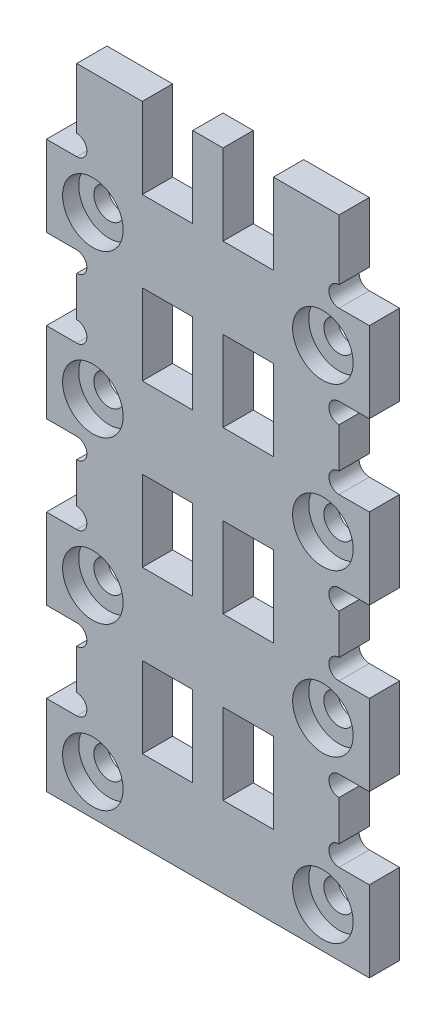
SolidWorks part; units mm, degrees
material "Thornel Mat VMA"
ref_plane "前视基准面" through (0, 0, 0) normal (0, 0, 1) x (1, 0, 0)
ref_plane "上视基准面" through (0, 0, 0) normal (0, 1, 0) x (1, 0, 0)
ref_plane "右视基准面" through (0, 0, 0) normal (1, 0, 0) x (0, 0, -1)
sketch "草图1" plane through (0, 0, 0) normal (0, 0, 1) x (1, 0, 0)
  line L0 (0, 0) -> (0, 16.7389) construction
  line L1 (16, 0) -> (-16, 0)
  line L2 (-16, 0) -> (-16, 8)
  line L3 (-16, 8) -> (-13, 8)
  line L4 (-13, 8) -> (-13, 16)
  line L5 (-13, 16) -> (-16, 16)
  line L6 (-16, 16) -> (-16, 24)
  line L7 (-16, 24) -> (-13, 24)
  line L8 (-13, 24) -> (-13, 32)
  line L9 (-13, 32) -> (-16, 32)
  line L10 (-16, 32) -> (-16, 40)
  line L11 (-16, 40) -> (-13, 40)
  line L12 (-13, 40) -> (-13, 48)
  line L13 (-13, 48) -> (-16, 48)
  line L14 (-16, 48) -> (-16, 56)
  line L15 (-16, 56) -> (-13, 56)
  line L16 (16, 0) -> (16, 8)
  line L17 (16, 8) -> (13, 8)
  line L18 (13, 8) -> (13, 16)
  line L19 (13, 16) -> (16, 16)
  line L20 (16, 16) -> (16, 24)
  line L21 (16, 24) -> (13, 24)
  line L22 (13, 24) -> (13, 32)
  line L23 (13, 32) -> (16, 32)
  line L24 (16, 32) -> (16, 40)
  line L25 (16, 40) -> (13, 40)
  line L26 (13, 40) -> (13, 48)
  line L27 (13, 48) -> (16, 48)
  line L28 (16, 48) -> (16, 56)
  line L29 (-13, 56) -> (-13, 64)
  line L30 (-13, 64) -> (13, 64)
  line L31 (16, 56) -> (13, 56)
  line L32 (13, 56) -> (13, 64)
  point P32 (0, 56)
  point P37 (0, 64)
  dimension "D1" = 16
  dimension "D2" = 8
  dimension "D3" = 3
  dimension "D4" = 8
  dimension "D5" = 8
  dimension "D6" = 8
  dimension "D7" = 8
  dimension "D8" = 3
  dimension "D9" = 8
  dimension "D10" = 8
  dimension "D11" = 16
  dimension "D12" = 8
  dimension "D13" = 3
extrude "凸台-拉伸1" add sketch "草图1" along normal blind 3
sketch "草图2" plane through (0, 0, 3) normal (0, 0, 1) x (1, 0, 0)
  line L0 (-13, 12) -> (13, 12) construction
  line L1 (-13, 16) -> (-13, 8) construction
  line L2 (13, 8) -> (13, 16) construction
  line L3 (-13, 28) -> (13, 28) construction
  line L4 (-13, 32) -> (-13, 24) construction
  line L5 (13, 24) -> (13, 32) construction
  line L6 (-13, 44) -> (13, 44) construction
  line L7 (-13, 48) -> (-13, 40) construction
  line L8 (13, 40) -> (13, 48) construction
  line L9 (-6.5, 32) -> (-6.5, 24)
  line L10 (-6.5, 16) -> (-1.5, 16)
  line L11 (-6.5, 16) -> (-6.5, 8)
  line L12 (-6.5, 8) -> (-1.5, 8)
  line L13 (-1.5, 16) -> (-1.5, 8)
  line L14 (-6.5, 16) -> (-1.5, 8) construction
  line L15 (-6.5, 8) -> (-1.5, 16) construction
  line L16 (-6.5, 32) -> (-1.5, 32)
  line L17 (-1.5, 32) -> (-1.5, 24)
  line L18 (-6.5, 24) -> (-1.5, 24)
  line L19 (1.5, 32) -> (1.5, 24)
  line L20 (6.5, 32) -> (1.5, 32)
  line L21 (6.5, 32) -> (6.5, 24)
  line L22 (6.5, 24) -> (1.5, 24)
  line L23 (0, 12) -> (0, 19.1819) construction
  line L24 (-6.5, 48) -> (-6.5, 40)
  line L25 (-6.5, 48) -> (-1.5, 48)
  line L26 (-1.5, 48) -> (-1.5, 40)
  line L27 (-6.5, 40) -> (-1.5, 40)
  line L28 (1.5, 48) -> (1.5, 40)
  line L29 (6.5, 48) -> (1.5, 48)
  line L30 (6.5, 48) -> (6.5, 40)
  line L31 (6.5, 40) -> (1.5, 40)
  line L32 (6.5, 8) -> (1.5, 8)
  line L33 (6.5, 16) -> (6.5, 8)
  line L34 (1.5, 16) -> (1.5, 8)
  line L35 (6.5, 16) -> (1.5, 16)
  line L36 (0, 64) -> (0, 54.9911) construction
  line L37 (13, 64) -> (-13, 64) construction
  line L38 (0, 60) -> (-4, 60) construction
  line L39 (6.5, 56) -> (1.5, 56)
  line L40 (-6.5, 64) -> (-1.5, 64)
  line L41 (-6.5, 64) -> (-6.5, 56)
  line L42 (-6.5, 56) -> (-1.5, 56)
  line L43 (-1.5, 64) -> (-1.5, 56)
  line L44 (-6.5, 64) -> (-1.5, 56) construction
  line L45 (-6.5, 56) -> (-1.5, 64) construction
  line L46 (1.5, 64) -> (1.5, 56)
  line L47 (6.5, 64) -> (1.5, 64)
  line L48 (6.5, 64) -> (6.5, 56)
  point P18 (0, 12)
  point P19 (0, 28)
  point P20 (0, 44)
  point P21 (-4, 12)
  dimension "D1" = 4
  dimension "D2" = 8
  dimension "D3" = 5
  dimension "D4" = 3
  dimension "D5" = 4
  dimension "D6" = 4
  dimension "D7" = 8
  dimension "D8" = 5
extrude "切除-拉伸1" cut sketch "草图2" against normal blind 3
sketch "草图3" plane through (0, 0, 3) normal (0, 0, 1) x (1, 0, 0)
  line L0 (-16, 4) -> (16, 4) construction
  line L1 (-16, 8) -> (-16, 0) construction
  line L2 (16, 0) -> (16, 8) construction
  line L3 (0, 4) -> (0, 12.4627) construction
  line L4 (-16, 20) -> (16, 20) construction
  line L5 (-16, 24) -> (-16, 16) construction
  line L6 (16, 16) -> (16, 24) construction
  circle A0 centre (-11.4, 4) radius 1.5
  circle A1 centre (11.4, 4) radius 1.5
  circle A2 centre (-11.4, 20) radius 1.5
  circle A3 centre (11.4, 20) radius 1.5
  circle A4 centre (-11.4, 36) radius 1.5
  circle A5 centre (11.4, 36) radius 1.5
  circle A6 centre (-11.4, 52) radius 1.5
  circle A7 centre (11.4, 52) radius 1.5
  point P6 (0, 4)
  point P7 (-11.4, 4)
  dimension "D2" = 3
  dimension "D1" = 11.4
  dimension "D3" = 4
extrude "切除-拉伸2" cut sketch "草图3" against normal blind 3
sketch "草图4" plane through (0, 0, 3) normal (0, 0, 1) x (1, 0, 0)
  circle A0 centre (-11.4, 4) radius 3
  circle A1 centre (11.4, 4) radius 3
  circle A2 centre (-11.4, 20) radius 3
  circle A3 centre (11.4, 20) radius 3
  circle A4 centre (-11.4, 36) radius 3
  circle A5 centre (11.4, 36) radius 3
  circle A6 centre (-11.4, 52) radius 3
  circle A7 centre (11.4, 52) radius 3
  dimension "D1" = 6
  dimension "D2" = 6
  dimension "D3" = 4
extrude "切除-拉伸3" cut sketch "草图4" against normal blind 1.6
sketch "草图5" plane through (0, 0, 3) normal (0, 0, 1) x (1, 0, 0)
  line L0 (-13, 64) -> (-13, 56) construction
  line L1 (-13, 48) -> (-13, 40) construction
  line L2 (-13, 32) -> (-13, 24) construction
  line L3 (-13, 16) -> (-13, 8) construction
  line L4 (0, 0) -> (0, 12.4589) construction
  line L5 (-16, 0) -> (16, 0) construction
  circle A0 centre (-13, 57.005) radius 1.005
  circle A1 centre (-13, 46.995) radius 1.005
  circle A2 centre (-13, 41.005) radius 1.005
  circle A3 centre (-13, 30.995) radius 1.005
  circle A4 centre (-13, 25.005) radius 1.005
  circle A5 centre (-13, 14.995) radius 1.005
  circle A6 centre (-13, 9.005) radius 1.005
  circle A7 centre (13, 9.005) radius 1.005
  circle A8 centre (13, 14.995) radius 1.005
  circle A9 centre (13, 25.005) radius 1.005
  circle A10 centre (13, 30.995) radius 1.005
  circle A11 centre (13, 41.005) radius 1.005
  circle A12 centre (13, 46.995) radius 1.005
  circle A13 centre (13, 57.005) radius 1.005
  dimension "D1" = 2.01
  dimension "D2" = 2.01
  dimension "D3" = 2.01
  dimension "D4" = 2.01
  dimension "D5" = 2.01
  dimension "D6" = 2.01
  dimension "D7" = 2.01
extrude "切除-拉伸4" cut sketch "草图5" against normal up to next
